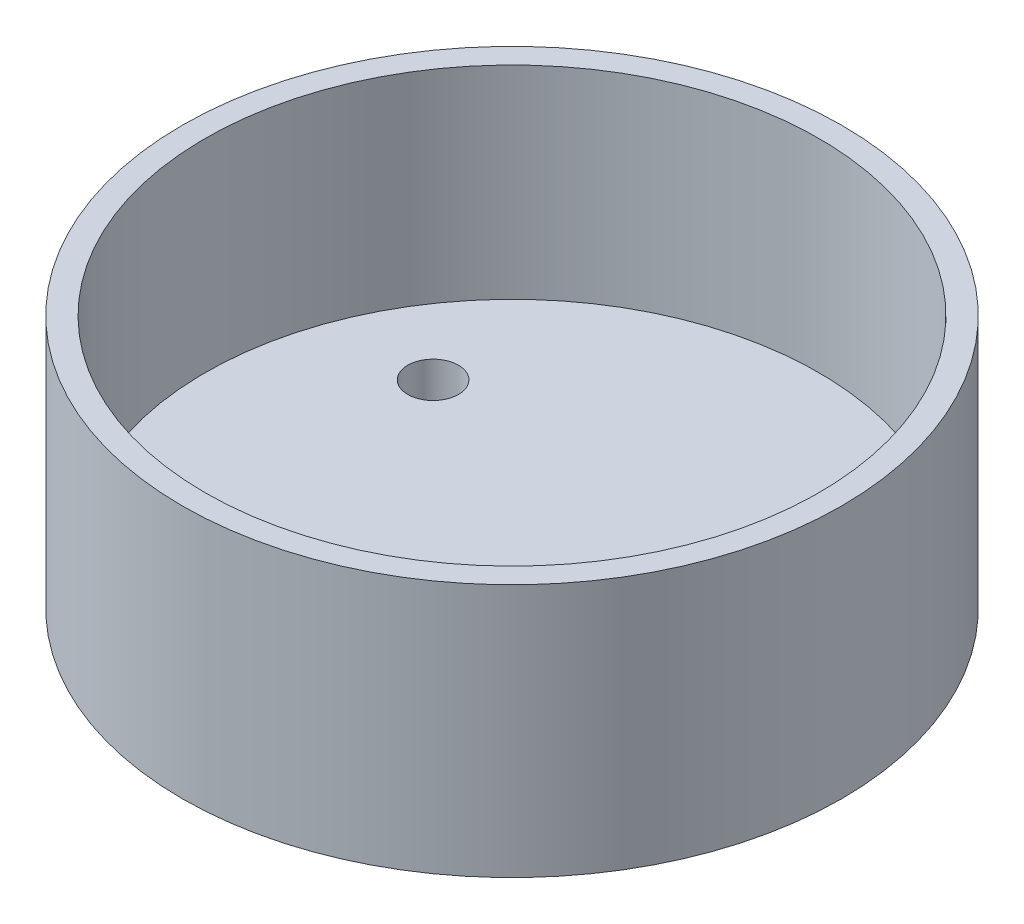
SolidWorks part; units mm, degrees
ref_plane "Front Plane" through (0, 0, 0) normal (0, 0, 1) x (1, 0, 0)
ref_plane "Top Plane" through (0, 0, 0) normal (0, 1, 0) x (1, 0, 0)
ref_plane "Right Plane" through (0, 0, 0) normal (1, 0, 0) x (0, 0, -1)
sketch "Sketch2" plane through (0, 0, 0) normal (0, 1, 0) x (1, 0, 0)
  circle A1 centre (0, 0) radius 13
  dimension "D2" = 26
extrude "Boss-Extrude2" add sketch "Sketch2" along normal blind 10 contours A1
sketch "Sketch5" plane through (0, 10, 0) normal (0, 1, 0) x (1, 0, 0)
  circle A0 centre (0, 0) radius 12.1
  dimension "D1" = 24.2
extrude "Cut-Extrude2" cut sketch "Sketch5" against normal blind 8
sketch "Sketch6" plane through (0, 2, 0) normal (0, 1, 0) x (1, 0, 0)
  line L0 (0, 14.0503) -> (0, -14.1228) construction
  line L1 (0, 0) -> (0, -8.5)
  line L4 (-8.5, 0) -> (8.5, 0)
  circle A0 centre (0, 0) radius 8.5
  circle A1 centre (0, -8.5) radius 1
  circle A2 centre (-7.3612, 4.25) radius 1
  circle A3 centre (7.3612, 4.25) radius 1
  circle A4 centre (0, 8.5) radius 2.608
  dimension "D1" = 17
  dimension "D4" = 2
  dimension "D5" = 2
  dimension "D6" = 2
  dimension "D2" = 4.25
  dimension "D3" = 4.25
extrude "Cut-Extrude3" cut sketch "Sketch6" against normal blind 8 contours A0 A2 | A0 A2 | A0 A3 | A0 A3 | A0 A1 L1 | L1 A1 A0 | L0 A0 A1 | A0 L0 A1
